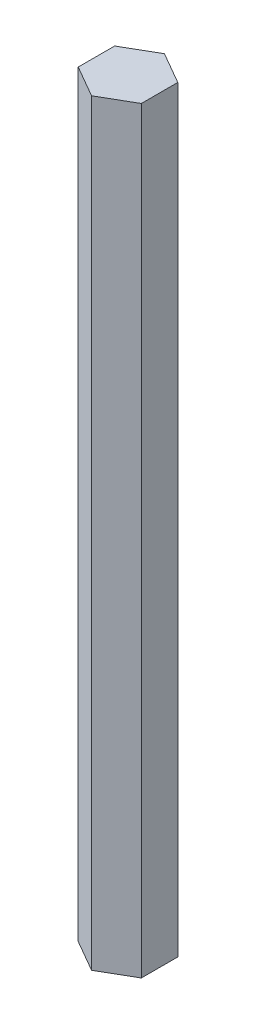
SolidWorks part; units mm, degrees
ref_plane "Front Plane" through (0, 0, 0) normal (0, 0, 1) x (1, 0, 0)
ref_plane "Top Plane" through (0, 0, 0) normal (0, 1, 0) x (1, 0, 0)
ref_plane "Right Plane" through (0, 0, 0) normal (1, 0, 0) x (0, 0, -1)
sketch "Sketch1" plane through (0, 0, 0) normal (0, 1, 0) x (1, 0, 0)
  line L1 (6.35, 3.6662) -> (0, 7.3323)
  line L2 (0, 7.3323) -> (-6.35, 3.6662)
  line L3 (-6.35, 3.6662) -> (-6.35, -3.6662)
  line L4 (-6.35, -3.6662) -> (0, -7.3323)
  line L5 (0, -7.3323) -> (6.35, -3.6662)
  line L6 (6.35, -3.6662) -> (6.35, 3.6662)
  circle A1 centre (0, 0) radius 6.35 construction
  point P1 (0, 0)
  dimension "D1" = 12.7
extrude "Boss-Extrude2" add sketch "Sketch1" along normal blind 152.4
